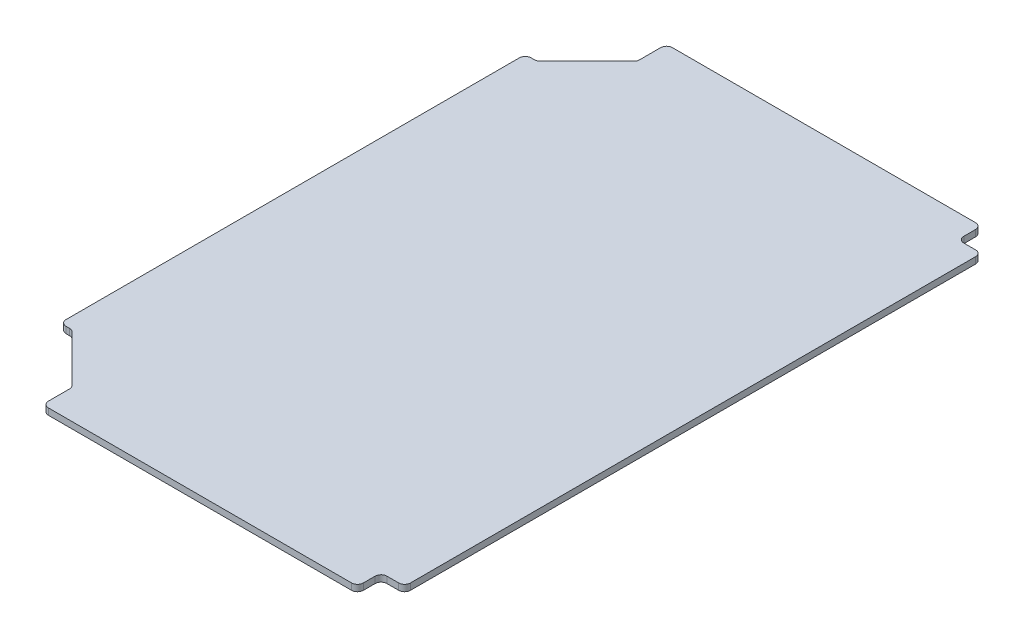
SolidWorks part; units mm, degrees
ref_plane "Front Plane" through (0, 0, 0) normal (0, 0, 1) x (1, 0, 0)
ref_plane "Top Plane" through (0, 0, 0) normal (0, 1, 0) x (1, 0, 0)
ref_plane "Right Plane" through (0, 0, 0) normal (1, 0, 0) x (0, 0, -1)
sketch "Sketch1" plane through (0, 0, 0) normal (0, 1, 0) x (1, 0, 0)
  line L1 (0, 0) -> (190.5, 0)
  line L2 (0, 0) -> (0, 304.8)
  line L3 (0, 304.8) -> (190.5, 304.8)
  line L4 (190.5, 0) -> (190.5, 304.8)
  dimension "D1" = 304.8
  dimension "D2" = 190.5
extrude "Boss-Extrude1" add sketch "Sketch1" along normal blind 2.7781
sketch "Sketch2" plane through (0, 2.7781, 0) normal (0, 1, 0) x (1, 0, 0)
  line L0 (190.5, 0) -> (190.5, 304.8) construction
  line L1 (0, 0) -> (190.5, 0)
  line L2 (0, 0) -> (0, 17.78)
  line L3 (0, 17.78) -> (190.5, 17.78)
  line L4 (190.5, 0) -> (190.5, 17.78)
  line L6 (0, 304.8) -> (190.5, 304.8)
  line L7 (0, 304.8) -> (0, 287.02)
  line L8 (0, 287.02) -> (190.5, 287.02)
  line L9 (190.5, 304.8) -> (190.5, 287.02)
  dimension "D1" = 17.78
  dimension "D2" = 17.78
extrude "Cut-Extrude1" cut sketch "Sketch2" against normal through all
sketch "Sketch3" plane through (0, 2.7781, 0) normal (0, 1, 0) x (1, 0, 0)
  line L0 (190.5, 17.78) -> (0, 17.78) construction
  line L1 (0, 287.02) -> (17.78, 287.02)
  line L2 (0, 287.02) -> (0, 17.78)
  line L3 (0, 17.78) -> (17.78, 17.78)
  line L4 (17.78, 287.02) -> (17.78, 17.78)
  dimension "D1" = 17.78
extrude "Cut-Extrude2" cut sketch "Sketch3" against normal through all
sketch "Sketch4" plane through (0, 2.7781, 0) normal (0, 1, 0) x (1, 0, 0)
  line L0 (22.86, 252.73) -> (44.45, 274.32)
  line L1 (17.78, 17.78) -> (17.78, 287.02) construction
  line L4 (22.86, 52.07) -> (44.45, 30.48)
  line L7 (17.78, 247.65) -> (17.78, 57.15) construction
  line L8 (44.45, 274.32) -> (44.45, 287.02)
  line L9 (17.78, 287.02) -> (190.5, 287.02) construction
  line L10 (44.45, 287.02) -> (17.78, 287.02)
  line L11 (17.78, 287.02) -> (17.78, 252.73)
  line L12 (44.45, 30.48) -> (44.45, 17.78)
  line L13 (190.5, 17.78) -> (17.78, 17.78) construction
  line L14 (44.45, 17.78) -> (17.78, 17.78)
  line L15 (17.78, 17.78) -> (17.78, 52.07)
  line L16 (22.86, 252.73) -> (17.78, 252.73)
  line L17 (22.86, 52.07) -> (17.78, 52.07)
  point P7 (17.78, 152.4)
  point P9 (17.78, 152.4)
  dimension "D1" = 45
  dimension "D2" = 26.67
  dimension "D3" = 190.5
  dimension "D4" = 26.67
  dimension "D5" = 5.08
  dimension "D6" = 34.29
  dimension "D7" = 34.29
  dimension "D8" = 5.08
extrude "Cut-Extrude3" cut sketch "Sketch4" against normal through all
sketch "Sketch5" plane through (0, 2.7781, 0) normal (0, 1, 0) x (1, 0, 0)
  line L1 (190.5, 287.02) -> (180.34, 287.02)
  line L2 (190.5, 287.02) -> (190.5, 276.86)
  line L3 (190.5, 276.86) -> (180.34, 276.86)
  line L4 (180.34, 287.02) -> (180.34, 276.86)
  line L5 (190.5, 17.78) -> (180.34, 17.78)
  line L6 (190.5, 17.78) -> (190.5, 27.94)
  line L7 (190.5, 27.94) -> (180.34, 27.94)
  line L8 (180.34, 17.78) -> (180.34, 27.94)
  dimension "D1" = 10.16
extrude "Cut-Extrude4" cut sketch "Sketch5" against normal through all
fillet "Fillet1" radius 2.54 14 edges at (44.45, 1.3891, -17.78) (44.45, 1.3891, -30.48) (44.45, 1.3891, -274.32) (44.45, 1.3891, -287.02) (17.78, 1.3891, -252.73) (22.86, 1.3891, -252.73) (17.78, 1.3891, -52.07) (22.86, 1.3891, -52.07) (180.34, 1.3891, -17.78) (180.34, 1.3891, -27.94) (190.5, 1.3891, -27.94) (190.5, 1.3891, -276.86) (180.34, 1.3891, -276.86) (180.34, 1.3891, -287.02)
